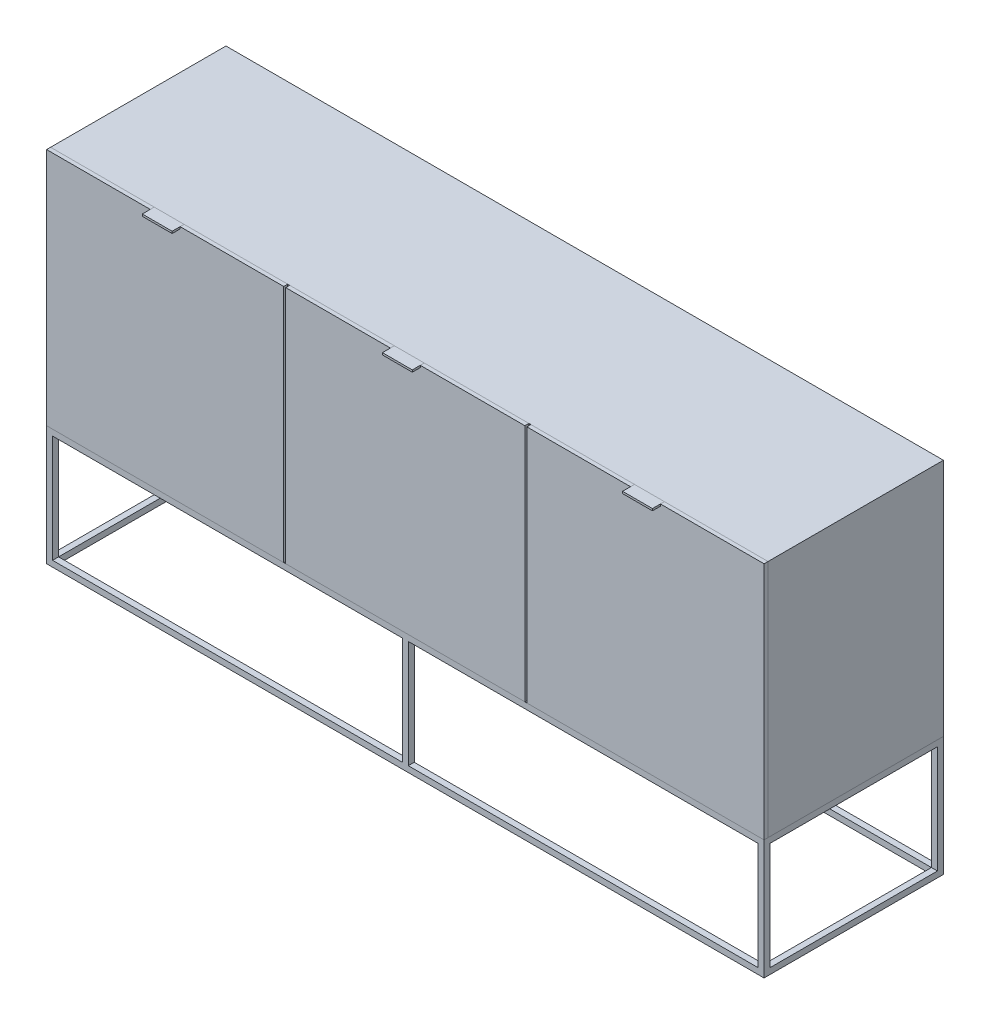
SolidWorks part; units mm, degrees
ref_plane "Alzado" through (0, 0, 0) normal (0, 0, 1) x (1, 0, 0)
ref_plane "Planta" through (0, 0, 0) normal (0, 1, 0) x (1, 0, 0)
ref_plane "Vista lateral" through (0, 0, 0) normal (1, 0, 0) x (0, 0, -1)
sketch "Croquis1" plane through (0, 0, 0) normal (0, 0, 1) x (1, 0, 0)
  line L0 (15, 285) -> (1785, 285)
  line L1 (0, 0) -> (1800, 0)
  line L2 (0, 0) -> (0, 300)
  line L3 (0, 300) -> (1800, 300)
  line L4 (1800, 0) -> (1800, 300)
  line L5 (1785, 15) -> (1785, 285)
  line L6 (15, 15) -> (1785, 15)
  line L7 (15, 15) -> (15, 285)
  dimension "D1" = 1800
  dimension "D2" = 300
  dimension "D3" = 15
extrude "Saliente-Extruir1" add sketch "Croquis1" against normal blind 450
sketch "Croquis2" plane through (0, 0, 0) normal (1, 0, 0) x (0, 0, -1)
  line L0 (435, 285) -> (15, 285)
  line L1 (15, 285) -> (15, 15)
  line L2 (15, 15) -> (435, 15)
  line L3 (435, 15) -> (435, 285)
  line L4 (0, 300) -> (0, 0)
  line L5 (0, 0) -> (450, 0)
  line L6 (450, 0) -> (450, 300)
  line L7 (450, 300) -> (0, 300)
  line L8 (0, 300) -> (0, 0)
  line L9 (0, 0) -> (450, 0)
  line L10 (450, 0) -> (450, 300)
  line L11 (450, 300) -> (0, 300)
  dimension "D1" = 0
  dimension "D2" = 15
extrude "Cortar-Extruir1" cut sketch "Croquis2" along normal blind 1900 contours L2 L3 L0 L1
sketch "Croquis3" plane through (0, 0, 0) normal (0, 1, 0) x (1, 0, 0)
  line L0 (1785, 435) -> (15, 435)
  line L1 (15, 435) -> (15, 15)
  line L2 (15, 15) -> (1785, 15)
  line L3 (1785, 15) -> (1785, 435)
  line L4 (0, 0) -> (1800, 0)
  line L5 (1800, 0) -> (1800, 450)
  line L6 (1800, 450) -> (0, 450)
  line L7 (0, 450) -> (0, 0)
  line L8 (0, 0) -> (1800, 0)
  line L9 (1800, 0) -> (1800, 450)
  line L10 (1800, 450) -> (0, 450)
  line L11 (0, 450) -> (0, 0)
  dimension "D1" = 0
  dimension "D2" = 15
extrude "Cortar-Extruir2" cut sketch "Croquis3" along normal blind 400 contours L2 L3 L0 L1
sketch "Croquis4" plane through (0, 0, 0) normal (0, 0, 1) x (1, 0, 0)
  line L1 (0, 300) -> (1800, 300)
  line L2 (0, 300) -> (0, 900)
  line L3 (0, 900) -> (1800, 900)
  line L4 (1800, 300) -> (1800, 900)
  dimension "D1" = 1800
  dimension "D2" = 600
extrude "Saliente-Extruir2" add sketch "Croquis4" against normal blind 440 from offset 10 separate body offset against normal yes
shell "Vaciado1" thickness 10
sketch "Croquis5" plane through (0, 0, 0) normal (0, 0, 1) x (1, 0, 0)
  line L0 (0, 300) -> (1800, 300) construction
  line L1 (0, 900) -> (595, 900)
  line L2 (0, 900) -> (0, 300)
  line L3 (0, 300) -> (595, 300)
  line L4 (595, 900) -> (595, 300)
  line L5 (1800, 900) -> (0, 900) construction
  line L6 (600, 900) -> (1200, 900)
  line L7 (600, 900) -> (600, 300)
  line L8 (600, 300) -> (1200, 300)
  line L9 (1200, 900) -> (1200, 300)
  line L10 (1800, 300) -> (0, 300) construction
  line L11 (1800, 900) -> (1205, 900)
  line L12 (1800, 900) -> (1800, 300)
  line L13 (1800, 300) -> (1205, 300)
  line L14 (1205, 900) -> (1205, 300)
  line L15 (1790, 890) -> (10, 890) construction
  point P22 (900, 890)
  point P23 (900, 900)
  dimension "D1" = 5
  dimension "D2" = 5
  dimension "D3" = 595
extrude "Saliente-Extruir3" add sketch "Croquis5" against normal blind 10 separate body
sketch "Croquis6" plane through (0, 0, 0) normal (0, 1, 0) x (1, 0, 0)
  line L0 (0, 0) -> (1800, 0) construction
  line L1 (907.5, 0) -> (892.5, 0)
  line L2 (907.5, 0) -> (907.5, 15)
  line L3 (907.5, 15) -> (892.5, 15)
  line L4 (892.5, 0) -> (892.5, 15)
  line L5 (15, 15) -> (1785, 15) construction
  line L6 (1785, 435) -> (15, 435) construction
  line L7 (892.5, 435) -> (907.5, 435)
  line L8 (892.5, 435) -> (892.5, 450)
  line L9 (892.5, 450) -> (907.5, 450)
  line L10 (907.5, 435) -> (907.5, 450)
  line L11 (0, 450) -> (1800, 450) construction
  point P16 (900, 0)
  point P17 (900, 0)
  dimension "D1" = 15
extrude "Saliente-Extruir4" add sketch "Croquis6" along normal blind 300
sketch "Croquis7" plane through (0, 0, 0) normal (0, 0, 1) x (1, 0, 0)
  line L0 (595, 900) -> (0, 900) construction
  line L1 (592.5, 900) -> (602.5, 900)
  line L2 (592.5, 900) -> (592.5, 300)
  line L3 (592.5, 300) -> (602.5, 300)
  line L4 (602.5, 900) -> (602.5, 300)
  line L5 (600, 300) -> (1200, 300) construction
  line L6 (1200, 900) -> (600, 900) construction
  line L7 (1197.5, 900) -> (1207.5, 900)
  line L8 (1197.5, 900) -> (1197.5, 300)
  line L9 (1197.5, 300) -> (1207.5, 300)
  line L10 (1207.5, 900) -> (1207.5, 300)
  line L11 (1800, 300) -> (0, 300) construction
  line L12 (1200, 300) -> (1200, 900) construction
  line L13 (595, 300) -> (595, 900) construction
  dimension "D1" = 2.5
  dimension "D2" = 10
  dimension "D3" = 2.5
  dimension "D4" = 10
extrude "Saliente-Extruir5" add sketch "Croquis7" against normal up to surface (430 mm away) from offset 10 up to face at (900, 600, -440) offset against normal yes
sketch "Croquis8" plane through (0, 0, 0) normal (0, 1, 0) x (1, 0, 0)
  line L0 (595, 0) -> (0, 0) construction
  line L1 (260, 0) -> (335, 0)
  line L2 (260, 0) -> (260, 10)
  line L3 (260, 10) -> (335, 10)
  line L4 (335, 0) -> (335, 10)
  line L5 (1200, 0) -> (600, 0) construction
  line L6 (862.5, 0) -> (937.5, 0)
  line L7 (862.5, 0) -> (862.5, 10)
  line L8 (862.5, 10) -> (937.5, 10)
  line L9 (937.5, 0) -> (937.5, 10)
  line L10 (1800, 0) -> (1205, 0) construction
  line L11 (1465, 0) -> (1540, 0)
  line L12 (1465, 0) -> (1465, 10)
  line L13 (1465, 10) -> (1540, 10)
  line L14 (1540, 0) -> (1540, 10)
  line L15 (595, 10) -> (0, 10) construction
  line L16 (1200, 10) -> (600, 10) construction
  line L18 (1800, 10) -> (1205, 10) construction
  point P20 (297.5, 10)
  point P21 (297.5, 0)
  point P24 (900, 10)
  point P25 (900, 0)
  point P30 (1502.5, 10)
  point P31 (1502.5, 0)
  dimension "D1" = 75
  dimension "D2" = 75
  dimension "D3" = 75
  dimension "D4" = 10
  dimension "D5" = 10
  dimension "D6" = 10
extrude "Cortar-Extruir3" cut sketch "Croquis8" against normal blind 5 from vertex
sketch "Croquis9" plane through (0, 0, 0) normal (0, 1, 0) x (1, 0, 0)
  line L0 (335, 0) -> (335, 10) construction
  line L1 (260, 10) -> (335, 10)
  line L2 (260, 10) -> (260, -20)
  line L3 (260, -20) -> (335, -20)
  line L4 (335, 10) -> (335, -20)
  line L5 (862.5, 10) -> (937.5, 10)
  line L6 (862.5, 10) -> (862.5, -20)
  line L7 (862.5, -20) -> (937.5, -20)
  line L8 (937.5, 10) -> (937.5, -20)
  line L9 (1465, 10) -> (1540, 10)
  line L10 (1465, 10) -> (1465, -20)
  line L11 (1465, -20) -> (1540, -20)
  line L12 (1540, 10) -> (1540, -20)
  line L13 (937.5, 0) -> (937.5, 10) construction
  line L14 (1540, 0) -> (1540, 10) construction
  dimension "D1" = 30
  dimension "D2" = 30
  dimension "D3" = 30
extrude "Saliente-Extruir6" add sketch "Croquis9" against normal blind 5 from vertex at 900 separate body starting at point (1465, 900, 0)
